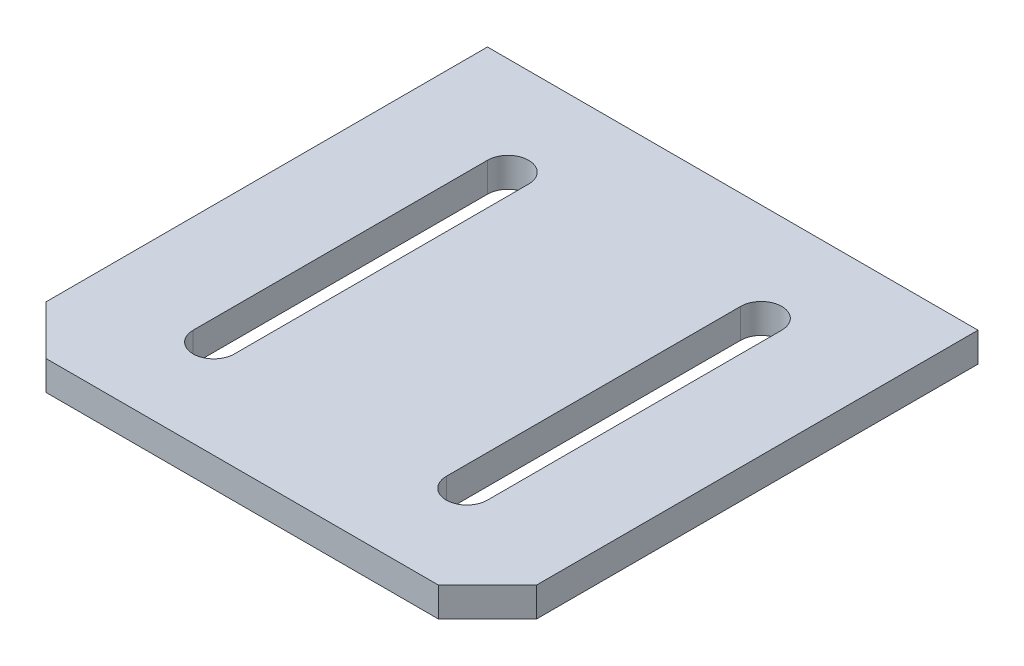
SolidWorks part; units mm, degrees
ref_plane "Alzado" through (0, 0, 0) normal (0, 0, 1) x (1, 0, 0)
ref_plane "Planta" through (0, 0, 0) normal (0, 1, 0) x (1, 0, 0)
ref_plane "Vista lateral" through (0, 0, 0) normal (1, 0, 0) x (0, 0, -1)
sketch "Sketch1" plane through (0, 0, 0) normal (0, 1, 0) x (1, 0, 0)
  line L1 (-25, -25) -> (25, -25)
  line L2 (-25, -25) -> (-25, 25)
  line L3 (-25, 25) -> (25, 25)
  line L4 (25, -25) -> (25, 25)
  line L5 (-25, -25) -> (25, 25) construction
  line L6 (-25, 25) -> (25, -25) construction
  point P0 (0, 0)
  dimension "D1" = 50
  dimension "D2" = 50
extrude "Boss-Extrude1" add sketch "Sketch1" along normal blind 3
chamfer "Chamfer1" distance 5 angle 45 2 edges at (25, 1.5, 25) (-25, 1.5, 25)
sketch "Sketch2" plane through (0, 3, 0) normal (0, 1, 0) x (1, 0, 0)
  line L0 (25, 25) -> (12.9, 25) construction
  line L1 (25, 25) -> (-25, 25) construction
  line L2 (12.9, 25) -> (12.9, 15) construction
  line L3 (0, 25) -> (0, -25) construction
  line L4 (-20, -25) -> (20, -25) construction
  line L5 (25, -20) -> (25, 25) construction
  line L6 (10.8, 15) -> (15, 15)
  line L7 (10.8, 15) -> (10.8, -15)
  line L8 (10.8, -15) -> (15, -15)
  line L9 (15, 15) -> (15, -15)
  line L10 (-10.8, 15) -> (-15, 15)
  line L11 (-15, 15) -> (-15, -15)
  line L12 (-10.8, -15) -> (-15, -15)
  line L13 (-10.8, 15) -> (-10.8, -15)
  circle A0 centre (12.9, 15) radius 2.1
  circle A1 centre (-12.9, 15) radius 2.1
  circle A2 centre (12.9, -15) radius 2.1
  circle A3 centre (-12.9, -15) radius 2.1
  dimension "D3" = 30
  dimension "D1" = 10
  dimension "D2" = 12.1
  dimension "D4" = 10
extrude "Cut-Extrude1" cut sketch "Sketch2" against normal blind 10 contours L11 A3 L13 A1 | A1 L10 | A1 L10 | A3 L12 | A3 L12 | L8 A2 | L8 A2 | A2 L9 A0 L7 | L6 A0 | L6 A0
